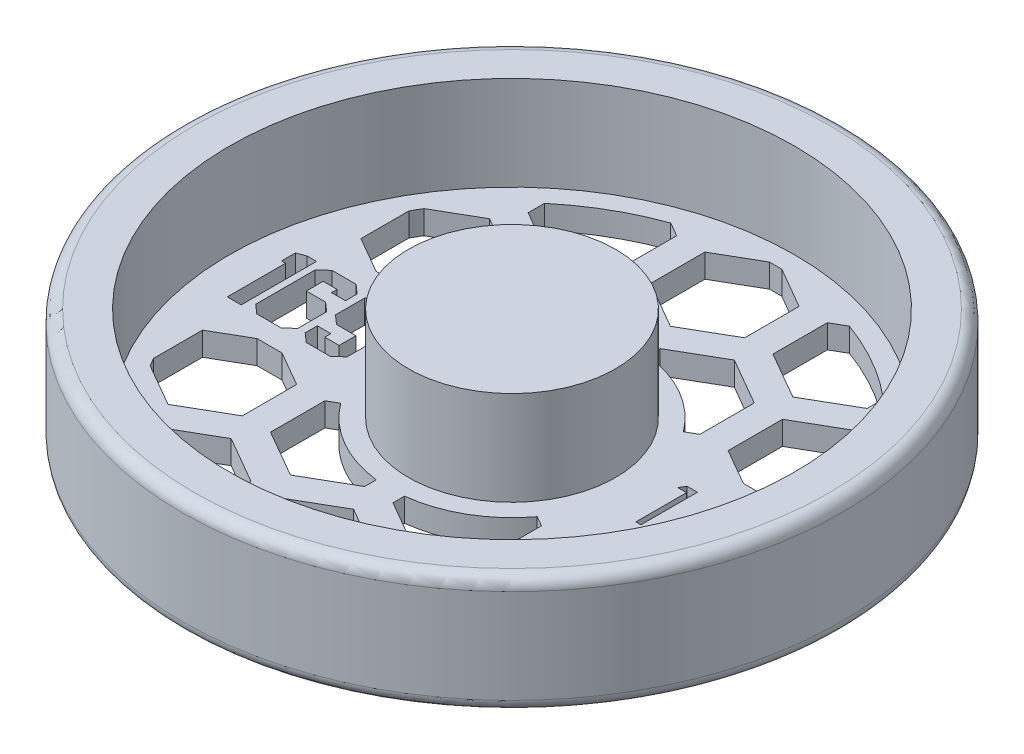
SolidWorks part; units mm, degrees
ref_plane "Front Plane" through (0, 0, 0) normal (0, 0, 1) x (1, 0, 0)
ref_plane "Top Plane" through (0, 0, 0) normal (0, 1, 0) x (1, 0, 0)
ref_plane "Right Plane" through (0, 0, 0) normal (1, 0, 0) x (0, 0, -1)
sketch "Sketch1" plane through (0, 0, 0) normal (0, 0, 1) x (1, 0, 0)
  line L0 (0, 0) -> (0, 15.875)
  line L1 (0, 15.875) -> (13.97, 15.875)
  line L2 (13.97, 15.875) -> (13.97, 3.175)
  line L3 (13.97, 3.175) -> (38.1, 3.175)
  line L4 (38.1, 3.175) -> (38.1, 15.875)
  line L5 (38.1, 15.875) -> (42.8625, 15.875)
  line L6 (44.45, 14.2875) -> (44.45, 1.5875)
  line L7 (42.8625, 0) -> (0, 0)
  arc A0 (42.8625, 0) -> (44.45, 1.5875) centre (42.8625, 1.5875) ccw
  arc A1 (44.45, 14.2875) -> (42.8625, 15.875) centre (42.8625, 14.2875) ccw
  dimension "D7" = 1.5875
  dimension "D1" = 3.175
  dimension "D2" = 6.35
  dimension "D3" = 38.1
  dimension "D4" = 13.97
  dimension "D5" = 12.7
  dimension "D6" = 12.7
revolve "Revolve1" add sketch "Sketch1" angle 360 about L0
sketch "Sketch2" plane through (0, 3.175, 0) normal (0, 1, 0) x (1, 0, 0)
  line L0 (-13.97, 0) -> (-38.1, 0) construction
  line L1 (13.97, 0) -> (38.1, 0) construction
  line L2 (-13.97, -5.08) -> (-38.1, -5.08) construction
  line L3 (13.97, -3.81) -> (38.1, -3.81) construction
  circle A0 centre (0, 0) radius 13.97 construction
  circle A1 centre (0, 0) radius 13.97 construction
  circle A2 centre (0, 0) radius 38.1 construction
  circle A3 centre (0, 0) radius 38.1 construction
  text T0 "169" font "Jersey M54" height 10.16
  text T1 "1/2" font "Century Gothic" height 7.62
  dimension "D1" = 5.08
  dimension "D2" = 3.81
extrude "Cut-Extrude1" cut sketch "Sketch2" against normal through all both and the other way through all
sketch "Sketch3" plane through (0, 3.175, 0) normal (0, 1, 0) x (1, 0, 0)
  line L0 (0, -7.9375) -> (0, 7.9375)
  line L1 (-34.6628, 7.9375) -> (34.6628, 7.9375)
  line L2 (-34.6628, -7.9375) -> (34.6628, -7.9375)
  line L3 (16.51, -7.3323) -> (22.86, -3.6662)
  line L4 (0, -7.3323) -> (6.35, -3.6662)
  line L5 (6.35, -3.6662) -> (6.35, 3.6662)
  line L6 (6.35, 3.6662) -> (0, 7.3323)
  line L7 (0, 7.3323) -> (-6.35, 3.6662)
  line L8 (-6.35, 3.6662) -> (-6.35, -3.6662)
  line L9 (-6.35, -3.6662) -> (0, -7.3323)
  line L10 (8.255, -6.9657) -> (1.905, -10.6319)
  line L11 (1.905, -10.6319) -> (1.905, -17.9643)
  line L12 (1.905, -17.9643) -> (8.255, -21.6304)
  line L13 (8.255, -21.6304) -> (14.605, -17.9643)
  line L14 (14.605, -17.9643) -> (14.605, -10.6319)
  line L15 (14.605, -10.6319) -> (8.255, -6.9657)
  line L16 (22.86, -3.6662) -> (22.86, 3.6662)
  line L17 (22.86, 3.6662) -> (16.51, 7.3323)
  line L18 (16.51, 7.3323) -> (10.16, 3.6662)
  line L19 (10.16, 3.6662) -> (10.16, -3.6662)
  line L20 (10.16, -3.6662) -> (16.51, -7.3323)
  line L21 (24.765, -6.9657) -> (18.415, -10.6319)
  line L22 (18.415, -10.6319) -> (18.415, -17.9643)
  line L23 (18.415, -17.9643) -> (24.765, -21.6304)
  line L24 (24.765, -21.6304) -> (31.115, -17.9643)
  line L25 (31.115, -17.9643) -> (31.115, -10.6319)
  line L26 (31.115, -10.6319) -> (24.765, -6.9657)
  line L27 (33.02, -7.3323) -> (39.37, -3.6662)
  line L28 (39.37, -3.6662) -> (39.37, 3.6662)
  line L29 (39.37, 3.6662) -> (33.02, 7.3323)
  line L30 (33.02, 7.3323) -> (26.67, 3.6662)
  line L31 (26.67, 3.6662) -> (26.67, -3.6662)
  line L32 (26.67, -3.6662) -> (33.02, -7.3323)
  line L33 (41.275, -6.9657) -> (34.925, -10.6319)
  line L34 (34.925, -10.6319) -> (34.925, -17.9643)
  line L35 (34.925, -17.9643) -> (41.275, -21.6304)
  line L36 (41.275, -21.6304) -> (47.625, -17.9643)
  line L37 (47.625, -17.9643) -> (47.625, -10.6319)
  line L38 (47.625, -10.6319) -> (41.275, -6.9657)
  line L39 (-16.51, -7.3323) -> (-10.16, -3.6662)
  line L40 (-10.16, -3.6662) -> (-10.16, 3.6662)
  line L41 (-10.16, 3.6662) -> (-16.51, 7.3323)
  line L42 (-16.51, 7.3323) -> (-22.86, 3.6662)
  line L43 (-22.86, 3.6662) -> (-22.86, -3.6662)
  line L44 (-22.86, -3.6662) -> (-16.51, -7.3323)
  line L45 (-8.255, -6.9657) -> (-14.605, -10.6319)
  line L46 (-14.605, -10.6319) -> (-14.605, -17.9643)
  line L47 (-14.605, -17.9643) -> (-8.255, -21.6304)
  line L48 (-8.255, -21.6304) -> (-1.905, -17.9643)
  line L49 (-1.905, -17.9643) -> (-1.905, -10.6319)
  line L50 (-1.905, -10.6319) -> (-8.255, -6.9657)
  line L51 (-33.02, -7.3323) -> (-26.67, -3.6662)
  line L52 (-26.67, -3.6662) -> (-26.67, 3.6662)
  line L53 (-26.67, 3.6662) -> (-33.02, 7.3323)
  line L54 (-33.02, 7.3323) -> (-39.37, 3.6662)
  line L55 (-39.37, 3.6662) -> (-39.37, -3.6662)
  line L56 (-39.37, -3.6662) -> (-33.02, -7.3323)
  line L57 (-24.765, -6.9657) -> (-31.115, -10.6319)
  line L58 (-31.115, -10.6319) -> (-31.115, -17.9643)
  line L59 (-31.115, -17.9643) -> (-24.765, -21.6304)
  line L60 (-24.765, -21.6304) -> (-18.415, -17.9643)
  line L61 (-18.415, -17.9643) -> (-18.415, -10.6319)
  line L62 (-18.415, -10.6319) -> (-24.765, -6.9657)
  line L63 (-49.53, -7.3323) -> (-43.18, -3.6662)
  line L64 (-43.18, -3.6662) -> (-43.18, 3.6662)
  line L65 (-43.18, 3.6662) -> (-49.53, 7.3323)
  line L66 (-49.53, 7.3323) -> (-55.88, 3.6662)
  line L67 (-55.88, 3.6662) -> (-55.88, -3.6662)
  line L68 (-55.88, -3.6662) -> (-49.53, -7.3323)
  line L69 (-41.275, -6.9657) -> (-47.625, -10.6319)
  line L70 (-47.625, -10.6319) -> (-47.625, -17.9643)
  line L71 (-47.625, -17.9643) -> (-41.275, -21.6304)
  line L72 (-41.275, -21.6304) -> (-34.925, -17.9643)
  line L73 (-34.925, -17.9643) -> (-34.925, -10.6319)
  line L74 (-34.925, -10.6319) -> (-41.275, -6.9657)
  line L75 (0, 21.3697) -> (6.35, 25.0358)
  line L76 (6.35, 25.0358) -> (6.35, 32.3682)
  line L77 (6.35, 32.3682) -> (0, 36.0343)
  line L78 (0, 36.0343) -> (-6.35, 32.3682)
  line L79 (-6.35, 32.3682) -> (-6.35, 25.0358)
  line L80 (-6.35, 25.0358) -> (0, 21.3697)
  line L81 (8.255, 21.7363) -> (1.905, 18.0701)
  line L82 (1.905, 18.0701) -> (1.905, 10.7377)
  line L83 (1.905, 10.7377) -> (8.255, 7.0716)
  line L84 (8.255, 7.0716) -> (14.605, 10.7377)
  line L85 (14.605, 10.7377) -> (14.605, 18.0701)
  line L86 (14.605, 18.0701) -> (8.255, 21.7363)
  line L87 (16.51, 21.3697) -> (22.86, 25.0358)
  line L88 (22.86, 25.0358) -> (22.86, 32.3682)
  line L89 (22.86, 32.3682) -> (16.51, 36.0343)
  line L90 (16.51, 36.0343) -> (10.16, 32.3682)
  line L91 (10.16, 32.3682) -> (10.16, 25.0358)
  line L92 (10.16, 25.0358) -> (16.51, 21.3697)
  line L93 (24.765, 21.7363) -> (18.415, 18.0701)
  line L94 (18.415, 18.0701) -> (18.415, 10.7377)
  line L95 (18.415, 10.7377) -> (24.765, 7.0716)
  line L96 (24.765, 7.0716) -> (31.115, 10.7377)
  line L97 (31.115, 10.7377) -> (31.115, 18.0701)
  line L98 (31.115, 18.0701) -> (24.765, 21.7363)
  line L99 (33.02, 21.3697) -> (39.37, 25.0358)
  line L100 (39.37, 25.0358) -> (39.37, 32.3682)
  line L101 (39.37, 32.3682) -> (33.02, 36.0343)
  line L102 (33.02, 36.0343) -> (26.67, 32.3682)
  line L103 (26.67, 32.3682) -> (26.67, 25.0358)
  line L104 (26.67, 25.0358) -> (33.02, 21.3697)
  line L105 (41.275, 21.7363) -> (34.925, 18.0701)
  line L106 (34.925, 18.0701) -> (34.925, 10.7377)
  line L107 (34.925, 10.7377) -> (41.275, 7.0716)
  line L108 (41.275, 7.0716) -> (47.625, 10.7377)
  line L109 (47.625, 10.7377) -> (47.625, 18.0701)
  line L110 (47.625, 18.0701) -> (41.275, 21.7363)
  line L111 (-16.51, 21.3697) -> (-10.16, 25.0358)
  line L112 (-10.16, 25.0358) -> (-10.16, 32.3682)
  line L113 (-10.16, 32.3682) -> (-16.51, 36.0343)
  line L114 (-16.51, 36.0343) -> (-22.86, 32.3682)
  line L115 (-22.86, 32.3682) -> (-22.86, 25.0358)
  line L116 (-22.86, 25.0358) -> (-16.51, 21.3697)
  line L117 (-8.255, 21.7363) -> (-14.605, 18.0701)
  line L118 (-14.605, 18.0701) -> (-14.605, 10.7377)
  line L119 (-14.605, 10.7377) -> (-8.255, 7.0716)
  line L120 (-8.255, 7.0716) -> (-1.905, 10.7377)
  line L121 (-1.905, 10.7377) -> (-1.905, 18.0701)
  line L122 (-1.905, 18.0701) -> (-8.255, 21.7363)
  line L123 (-24.765, 21.7363) -> (-31.115, 18.0701)
  line L124 (-31.115, 18.0701) -> (-31.115, 10.7377)
  line L125 (-31.115, 10.7377) -> (-24.765, 7.0716)
  line L126 (-24.765, 7.0716) -> (-18.415, 10.7377)
  line L127 (-18.415, 10.7377) -> (-18.415, 18.0701)
  line L128 (-18.415, 18.0701) -> (-24.765, 21.7363)
  line L129 (-33.02, 21.3697) -> (-26.67, 25.0358)
  line L130 (-26.67, 25.0358) -> (-26.67, 32.3682)
  line L131 (-26.67, 32.3682) -> (-33.02, 36.0343)
  line L132 (-33.02, 36.0343) -> (-39.37, 32.3682)
  line L133 (-39.37, 32.3682) -> (-39.37, 25.0358)
  line L134 (-39.37, 25.0358) -> (-33.02, 21.3697)
  line L135 (-49.53, 21.3697) -> (-43.18, 25.0358)
  line L136 (-43.18, 25.0358) -> (-43.18, 32.3682)
  line L137 (-43.18, 32.3682) -> (-49.53, 36.0343)
  line L138 (-49.53, 36.0343) -> (-55.88, 32.3682)
  line L139 (-55.88, 32.3682) -> (-55.88, 25.0358)
  line L140 (-55.88, 25.0358) -> (-49.53, 21.3697)
  line L141 (-41.275, 21.7363) -> (-47.625, 18.0701)
  line L142 (-47.625, 18.0701) -> (-47.625, 10.7377)
  line L143 (-47.625, 10.7377) -> (-41.275, 7.0716)
  line L144 (-41.275, 7.0716) -> (-34.925, 10.7377)
  line L145 (-34.925, 10.7377) -> (-34.925, 18.0701)
  line L146 (-34.925, 18.0701) -> (-41.275, 21.7363)
  line L147 (0, -36.0343) -> (6.35, -32.3682)
  line L148 (6.35, -32.3682) -> (6.35, -25.0358)
  line L149 (6.35, -25.0358) -> (0, -21.3697)
  line L150 (0, -21.3697) -> (-6.35, -25.0358)
  line L151 (-6.35, -25.0358) -> (-6.35, -32.3682)
  line L152 (-6.35, -32.3682) -> (0, -36.0343)
  line L153 (8.255, -35.6677) -> (1.905, -39.3339)
  line L154 (1.905, -39.3339) -> (1.905, -46.6663)
  line L155 (1.905, -46.6663) -> (8.255, -50.3324)
  line L156 (8.255, -50.3324) -> (14.605, -46.6663)
  line L157 (14.605, -46.6663) -> (14.605, -39.3339)
  line L158 (14.605, -39.3339) -> (8.255, -35.6677)
  line L159 (16.51, -36.0343) -> (22.86, -32.3682)
  line L160 (22.86, -32.3682) -> (22.86, -25.0358)
  line L161 (22.86, -25.0358) -> (16.51, -21.3697)
  line L162 (16.51, -21.3697) -> (10.16, -25.0358)
  line L163 (10.16, -25.0358) -> (10.16, -32.3682)
  line L164 (10.16, -32.3682) -> (16.51, -36.0343)
  line L165 (24.765, -35.6677) -> (18.415, -39.3339)
  line L166 (18.415, -39.3339) -> (18.415, -46.6663)
  line L167 (18.415, -46.6663) -> (24.765, -50.3324)
  line L168 (24.765, -50.3324) -> (31.115, -46.6663)
  line L169 (31.115, -46.6663) -> (31.115, -39.3339)
  line L170 (31.115, -39.3339) -> (24.765, -35.6677)
  line L171 (33.02, -36.0343) -> (39.37, -32.3682)
  line L172 (39.37, -32.3682) -> (39.37, -25.0358)
  line L173 (39.37, -25.0358) -> (33.02, -21.3697)
  line L174 (33.02, -21.3697) -> (26.67, -25.0358)
  line L175 (26.67, -25.0358) -> (26.67, -32.3682)
  line L176 (26.67, -32.3682) -> (33.02, -36.0343)
  line L177 (41.275, -35.6677) -> (34.925, -39.3339)
  line L178 (34.925, -39.3339) -> (34.925, -46.6663)
  line L179 (34.925, -46.6663) -> (41.275, -50.3324)
  line L180 (41.275, -50.3324) -> (47.625, -46.6663)
  line L181 (47.625, -46.6663) -> (47.625, -39.3339)
  line L182 (47.625, -39.3339) -> (41.275, -35.6677)
  line L183 (-16.51, -36.0343) -> (-10.16, -32.3682)
  line L184 (-10.16, -32.3682) -> (-10.16, -25.0358)
  line L185 (-10.16, -25.0358) -> (-16.51, -21.3697)
  line L186 (-16.51, -21.3697) -> (-22.86, -25.0358)
  line L187 (-22.86, -25.0358) -> (-22.86, -32.3682)
  line L188 (-22.86, -32.3682) -> (-16.51, -36.0343)
  line L189 (-8.255, -35.6677) -> (-14.605, -39.3339)
  line L190 (-14.605, -39.3339) -> (-14.605, -46.6663)
  line L191 (-14.605, -46.6663) -> (-8.255, -50.3324)
  line L192 (-8.255, -50.3324) -> (-1.905, -46.6663)
  line L193 (-1.905, -46.6663) -> (-1.905, -39.3339)
  line L194 (-1.905, -39.3339) -> (-8.255, -35.6677)
  line L195 (-24.765, -35.6677) -> (-31.115, -39.3339)
  line L196 (-31.115, -39.3339) -> (-31.115, -46.6663)
  line L197 (-31.115, -46.6663) -> (-24.765, -50.3324)
  line L198 (-24.765, -50.3324) -> (-18.415, -46.6663)
  line L199 (-18.415, -46.6663) -> (-18.415, -39.3339)
  line L200 (-18.415, -39.3339) -> (-24.765, -35.6677)
  line L201 (-33.02, -36.0343) -> (-26.67, -32.3682)
  line L202 (-26.67, -32.3682) -> (-26.67, -25.0358)
  line L203 (-26.67, -25.0358) -> (-33.02, -21.3697)
  line L204 (-33.02, -21.3697) -> (-39.37, -25.0358)
  line L205 (-39.37, -25.0358) -> (-39.37, -32.3682)
  line L206 (-39.37, -32.3682) -> (-33.02, -36.0343)
  line L207 (-49.53, -36.0343) -> (-43.18, -32.3682)
  line L208 (-43.18, -32.3682) -> (-43.18, -25.0358)
  line L209 (-43.18, -25.0358) -> (-49.53, -21.3697)
  line L210 (-49.53, -21.3697) -> (-55.88, -25.0358)
  line L211 (-55.88, -25.0358) -> (-55.88, -32.3682)
  line L212 (-55.88, -32.3682) -> (-49.53, -36.0343)
  line L213 (-41.275, -35.6677) -> (-47.625, -39.3339)
  line L214 (-47.625, -39.3339) -> (-47.625, -46.6663)
  line L215 (-47.625, -46.6663) -> (-41.275, -50.3324)
  line L216 (-41.275, -50.3324) -> (-34.925, -46.6663)
  line L217 (-34.925, -46.6663) -> (-34.925, -39.3339)
  line L218 (-34.925, -39.3339) -> (-41.275, -35.6677)
  circle A0 centre (0, 0) radius 35.56
  circle A1 centre (0, 0) radius 16.51
  circle A2 centre (0, 0) radius 6.35 construction
  circle A3 centre (8.255, -14.2981) radius 6.35 construction
  point P7 (0, 0)
  point P10 (0, 7.9375)
  point P13 (0, -7.9375)
  dimension "D1" = 71.12
  dimension "D2" = 33.02
  dimension "D3" = 15.875
  dimension "D4" = 12.7
  dimension "D5" = 12.7
  dimension "D6" = 3.81
  dimension "D7" = 1.905
  dimension "D8" = 3
  dimension "D9" = 4
  dimension "D10" = 2
  dimension "D11" = 2
extrude "Cut-Extrude4" cut sketch "Sketch3" against normal through all both and the other way through all contours L113 A0 L115 L116 L111 L112 | L123 A0 L124 L125 L1 L126 L127 L128 | A1 L121 L122 L117 L118 L119 | L77 A0 L78 L79 L80 L75 L76 | L88 A0 L90 L91 L92 L87 | A1 L84 L85 L86 L81 L82 | L97 A0 L98 L93 L94 L95 L1 L96 | L24 A0 L25 L26 L2 L21 L22 L23 | A1 L11 L12 L13 L14 L15 | L164 A0 L160 L161 L162 L163 | L152 A0 L147 L148 L149 L150 L151 | A1 L45 L46 L47 L48 L49 | L187 A0 L183 L184 L185 L186 | L58 A0 L59 L60 L61 L62 L2 L57
